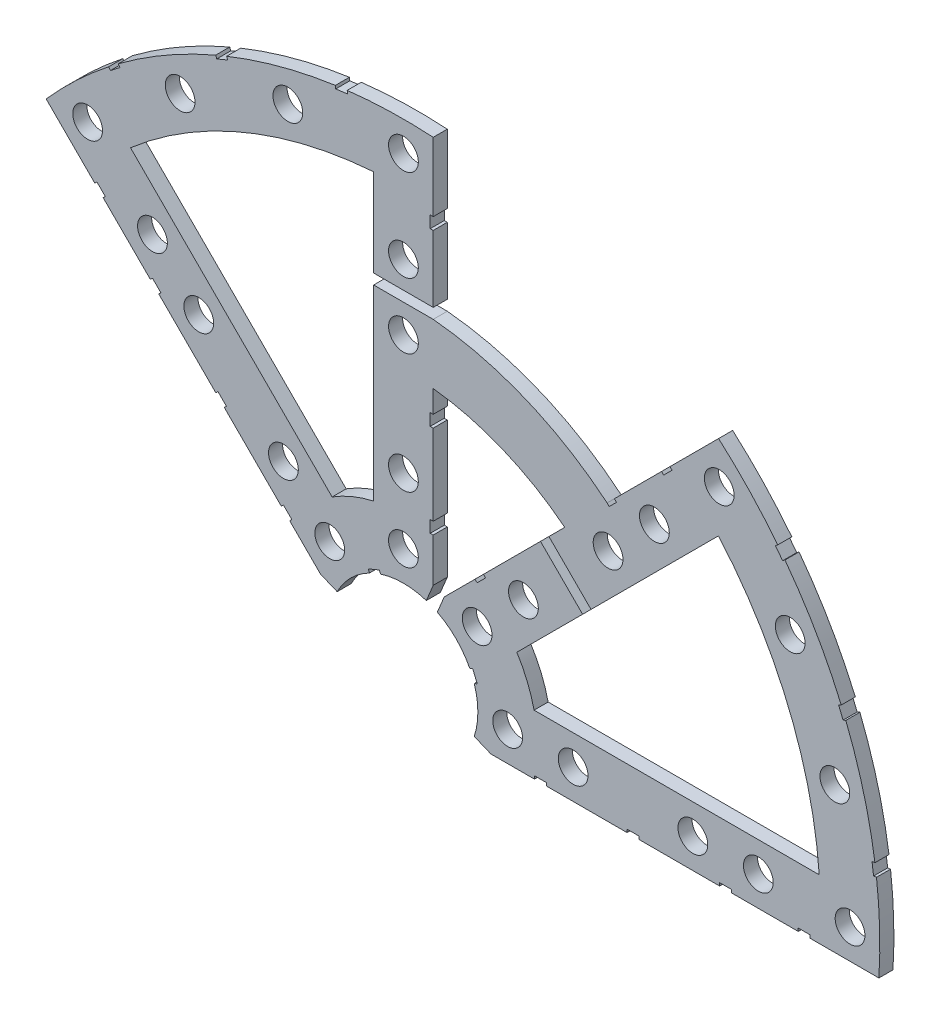
SolidWorks part; units mm, degrees
material "Brass"
ref_plane "Front Plane" through (0, 0, 0) normal (0, 0, 1) x (1, 0, 0)
ref_plane "Top Plane" through (0, 0, 0) normal (0, 1, 0) x (1, 0, 0)
ref_plane "Right Plane" through (0, 0, 0) normal (1, 0, 0) x (0, 0, -1)
sketch "Sketch1" plane through (0, 0, 0) normal (0, 0, 1) x (1, 0, 0)
  line L0 (0, 0) -> (320.3893, 0) construction
  line L1 (0, 0) -> (155.5285, 155.5285) construction
  line L2 (8.6967, 17.6769) -> (34.4055, 43.3857)
  line L3 (8.6967, 17.6769) -> (7.229, 14.1336)
  line L4 (101.4014, -6.35) -> (18.6489, -6.35)
  line L5 (15.1056, -4.8823) -> (18.6489, -6.35)
  line L6 (88.6729, 6.35) -> (27.8605, 6.35)
  line L7 (-76.1917, 67.2115) -> (-17.6769, 8.6967)
  line L8 (-58.2111, 67.1914) -> (-15.2102, 24.1905)
  line L9 (67.1914, 58.2111) -> (24.1905, 15.2102)
  line L10 (0, 0) -> (40.4486, 97.6516) construction
  line L11 (0, 0) -> (123.4567, -51.1374) construction
  line L12 (-6.35, 88.6729) -> (-6.35, 27.8605)
  line L13 (-17.6769, 8.6967) -> (-14.1336, 7.229)
  line L14 (4.8823, 15.1056) -> (6.35, 18.6489)
  line L15 (6.35, 18.6489) -> (6.35, 55.0067)
  line L16 (0, 0) -> (15.1056, -4.8823) construction
  line L17 (0, 0) -> (4.8823, 15.1056) construction
  line L18 (8.6967, 17.6769) -> (13.294, 8.6183) construction
  line L19 (18.6489, -6.35) -> (15.4943, 3.3063) construction
  line L20 (27.8605, 6.35) -> (27.7442, 6.7059) construction
  line L21 (24.1905, 15.2102) -> (24.3599, 14.8764) construction
  line L22 (6.35, 101.4014) -> (6.35, 18.6489) [skipped]
  line L23 (6.35, 67.7752) -> (6.35, 101.4014)
  line L24 (43.4342, 52.4144) -> (67.2115, 76.1917)
  line L25 (67.2115, 76.1917) -> (8.6967, 17.6769) construction
  arc A0 (7.229, 14.1336) -> (15.1056, -4.8823) centre (0, 0) cw
  arc A1 (67.2115, 76.1917) -> (101.4014, -6.35) centre (0, 0) cw
  arc A2 (24.1905, 15.2102) -> (27.8605, 6.35) centre (0, 0) cw
  arc A3 (67.1914, 58.2111) -> (88.6729, 6.35) centre (0, 0) cw
  arc A4 (-76.1917, 67.2115) -> (6.35, 101.4014) centre (0, 0) cw
  arc A5 (-58.2111, 67.1914) -> (-6.35, 88.6729) centre (0, 0) cw
  arc A6 (-15.2102, 24.1905) -> (-6.35, 27.8605) centre (0, 0) cw
  arc A7 (-14.1336, 7.229) -> (4.8823, 15.1056) centre (0, 0) cw
  arc A8 (13.294, 8.6183) -> (15.4943, 3.3063) centre (0, 0) cw construction
  arc A9 (24.3599, 14.8764) -> (27.7442, 6.7059) centre (0, 0) cw construction
  arc A10 (43.4342, 52.4144) -> (6.35, 67.7752) centre (0, 0) ccw
  arc A11 (34.4055, 43.3857) -> (6.35, 55.0067) centre (0, 0) ccw
  dimension "D1" = 45
  dimension "D3" = 6.35
  dimension "D4" = 15.875
  dimension "D7" = 22.5
  dimension "D8" = 101.6
  dimension "D11" = 12.7
  dimension "D12" = 12.7
  dimension "D15" = 12.7
  dimension "D16" = 55.372
  dimension "D2" = 6.35
  dimension "D5" = 67.5
  dimension "D9" = 1.27
  dimension "D10" = 1.27
  dimension "D14" = 90
  dimension "D6" = 12.7
  dimension "D13" = 2
extrude "Boss-Extrude1" add sketch "Sketch1" along normal blind 3
sketch "Sketch2" plane through (0, 0, 3) normal (0, 0, 1) x (1, 0, 0)
  line L0 (0, 0) -> (101.6, 0) construction
  line L1 (0, 0) -> (71.842, 71.842) construction
  line L2 (0, 0) -> (22.225, 0) construction
  line L3 (0, 0) -> (22.225, 0) construction
  line L4 (0, 0) -> (15.7154, 15.7154) construction
  line L5 (0, 0) -> (95.25, 0) construction
  line L6 (0, 0) -> (92.0044, 24.6525) construction
  line L7 (0, 0) -> (0, 22.225) construction
  line L8 (0, 0) -> (92.0044, 24.6525) construction
  line L9 (-76.1917, 67.2115) -> (-17.6769, 8.6967) construction
  line L10 (6.35, 67.7752) -> (6.35, 101.4014) construction
  arc A0 (101.4014, -6.35) -> (67.2115, 76.1917) centre (0, 0) ccw construction
  circle A1 centre (22.225, 0) radius 3.175
  arc A2 (15.1056, -4.8823) -> (7.229, 14.1336) centre (0, 0) ccw construction
  circle A3 centre (36.195, 0) radius 3.175
  circle A4 centre (61.722, 0) radius 3.175
  circle A5 centre (75.692, 0) radius 3.175
  circle A6 centre (95.25, 0) radius 3.175
  circle A7 centre (15.7154, 15.7154) radius 3.175
  circle A8 centre (25.5937, 25.5937) radius 3.175
  circle A9 centre (43.644, 43.644) radius 3.175
  circle A10 centre (53.5223, 53.5223) radius 3.175
  arc A11 (101.4014, -6.35) -> (67.2115, 76.1917) centre (0, 0) ccw construction
  circle A12 centre (92.0044, 24.6525) radius 3.175
  circle A13 centre (82.4889, 47.625) radius 3.175
  circle A14 centre (67.3519, 67.3519) radius 3.175
  circle A15 centre (47.625, 82.4889) radius 3.175 [skipped]
  circle A16 centre (24.6525, 92.0044) radius 3.175 [skipped]
  circle A17 centre (0, 95.25) radius 3.175
  circle A18 centre (0, 75.692) radius 3.175
  circle A19 centre (-53.5223, 53.5223) radius 3.175
  circle A20 centre (-43.644, 43.644) radius 3.175
  circle A21 centre (0, 61.722) radius 3.175
  circle A22 centre (0, 36.195) radius 3.175
  circle A23 centre (-25.5937, 25.5937) radius 3.175
  circle A24 centre (-15.7154, 15.7154) radius 3.175
  circle A25 centre (0, 22.225) radius 3.175
  circle A26 centre (-24.6525, 92.0044) radius 3.175
  circle A27 centre (-47.625, 82.4889) radius 3.175
  circle A28 centre (-67.3519, 67.3519) radius 3.175
  arc A29 (4.8823, 15.1056) -> (-14.1336, 7.229) centre (0, 0) ccw construction
  arc A30 (6.35, 101.4014) -> (-76.1917, 67.2115) centre (0, 0) ccw construction
  dimension "D3" = 6.35
  dimension "D1" = 45
  dimension "D2" = 6.35
  dimension "D5" = 13.97
  dimension "D7" = 13.97
  dimension "D9" = 45
  dimension "D14" = 90
  dimension "D4" = 6.35
  dimension "D8" = 19.558
  dimension "D11" = 15
  dimension "D6" = 25.527
  dimension "D15" = 15
  dimension "D16" = 6.35
  dimension "D17" = 6.35
  dimension "D18" = 6.35
  dimension "D19" = 6.35
  dimension "D20" = 6.35
  dimension "D12" = 2
  dimension "D13" = 2
  dimension "D10" = 10
extrude "Cut-Extrude1" cut sketch "Sketch2" against normal through all
sketch "Sketch3" plane through (0, 0, 3) normal (0, 0, 1) x (1, 0, 0)
  line L0 (15.2664, 24.2467) -> (17.0625, 26.0427)
  line L1 (15.2664, 24.2467) -> (15.7154, 23.7977)
  line L2 (17.0625, 26.0427) -> (17.5115, 25.5937)
  line L3 (15.7154, 23.7977) -> (17.5115, 25.5937)
  line L4 (55.049, 64.0292) -> (56.845, 65.8253)
  line L5 (34.4055, 43.3857) -> (8.6967, 17.6769) construction
  line L6 (29.2307, 38.211) -> (31.0268, 40.007)
  line L7 (29.2307, 38.211) -> (38.211, 29.2307)
  line L8 (31.0268, 40.007) -> (40.007, 31.0268)
  line L9 (27.94, -6.35) -> (30.48, -6.35)
  line L10 (27.94, -6.35) -> (27.94, -5.715)
  line L11 (30.48, -6.35) -> (30.48, -5.715)
  line L12 (27.94, -5.715) -> (30.48, -5.715)
  line L13 (18.6489, -6.35) -> (101.4014, -6.35) construction
  line L14 (67.437, -6.35) -> (69.977, -6.35)
  line L15 (67.437, -6.35) -> (67.437, -5.715)
  line L16 (69.977, -6.35) -> (69.977, -5.715)
  line L17 (67.437, -5.715) -> (69.977, -5.715)
  line L18 (38.211, 29.2307) -> (40.007, 31.0268)
  line L19 (55.049, 64.0292) -> (55.498, 63.5802)
  line L20 (56.845, 65.8253) -> (57.294, 65.3763)
  line L21 (55.498, 63.5802) -> (57.294, 65.3763)
  line L22 (67.2115, 76.1917) -> (43.4342, 52.4144) construction
  line L23 (43.4342, 52.4144) -> (44.9911, 53.9713)
  line L24 (43.4342, 52.4144) -> (43.8832, 51.9654)
  line L25 (44.9911, 53.9713) -> (45.4401, 53.5223)
  line L26 (47.6885, -6.35) -> (50.2285, -6.35)
  line L27 (47.6885, -6.35) -> (47.6885, -5.715)
  line L28 (50.2285, -6.35) -> (50.2285, -5.715)
  line L29 (47.6885, -5.715) -> (50.2285, -5.715)
  line L30 (84.201, -6.35) -> (86.741, -6.35)
  line L31 (84.201, -6.35) -> (84.201, -5.715)
  line L32 (86.741, -6.35) -> (86.741, -5.715)
  line L33 (84.201, -5.715) -> (86.741, -5.715)
  line L34 (0, 0) -> (100.7308, 13.2615) construction
  line L35 (0, 0) -> (93.8662, 38.8806) construction
  line L36 (0, 0) -> (80.6047, 61.8502) construction
  line L37 (0, 0) -> (101.6, 0) construction
  line L38 (99.9355, 14.4377) -> (100.267, 11.9194)
  line L39 (99.9355, 14.4377) -> (101.1946, 14.6035)
  line L40 (100.267, 11.9194) -> (101.5261, 12.0852)
  line L41 (101.1946, 14.6035) -> (101.5261, 12.0852)
  line L42 (99.9355, 14.4377) -> (101.5261, 12.0852) construction
  line L43 (100.267, 11.9194) -> (101.1946, 14.6035) construction
  line L44 (93.7655, 37.4643) -> (94.9388, 37.9503)
  line L45 (93.7655, 37.4643) -> (92.7935, 39.811)
  line L46 (94.9388, 37.9503) -> (93.9668, 40.297)
  line L47 (92.7935, 39.811) -> (93.9668, 40.297)
  line L48 (93.7655, 37.4643) -> (93.9668, 40.297) construction
  line L49 (94.9388, 37.9503) -> (92.7935, 39.811) construction
  line L50 (79.3278, 62.4712) -> (80.874, 60.456)
  line L51 (79.3278, 62.4712) -> (80.3354, 63.2443)
  line L52 (80.874, 60.456) -> (81.8816, 61.2292)
  line L53 (80.3354, 63.2443) -> (81.8816, 61.2292)
  line L54 (79.3278, 62.4712) -> (81.8816, 61.2292) construction
  line L55 (80.874, 60.456) -> (80.3354, 63.2443) construction
  line L56 (13.5939, 7.0054) -> (14.5659, 4.6588)
  line L57 (13.5939, 7.0054) -> (14.7672, 7.4914)
  line L58 (14.5659, 4.6588) -> (15.7393, 5.1448)
  line L59 (14.7672, 7.4914) -> (15.7393, 5.1448)
  line L60 (13.5939, 7.0054) -> (15.7393, 5.1448) construction
  line L61 (14.5659, 4.6588) -> (14.7672, 7.4914) construction
  line L62 (43.8832, 51.9654) -> (45.4401, 53.5223)
  line L63 (6.35, 67.7752) -> (6.35, 69.977)
  line L64 (-40.007, 31.0268) -> (-38.211, 29.2307)
  line L65 (-40.007, 31.0268) -> (-39.558, 31.4758)
  line L66 (-38.211, 29.2307) -> (-37.762, 29.6797)
  line L67 (-39.558, 31.4758) -> (-37.762, 29.6797)
  line L68 (-26.0427, 17.0625) -> (-25.5937, 17.5115)
  line L69 (-23.7977, 15.7154) -> (-25.5937, 17.5115)
  line L70 (-24.2467, 15.2664) -> (-26.0427, 17.0625)
  line L71 (-24.2467, 15.2664) -> (-23.7977, 15.7154)
  line L72 (-65.8253, 56.845) -> (-64.0292, 55.049)
  line L73 (-65.3763, 57.294) -> (-63.5802, 55.498)
  line L74 (-64.0292, 55.049) -> (-63.5802, 55.498)
  line L75 (-65.8253, 56.845) -> (-65.3763, 57.294)
  line L76 (-63.2443, 80.3354) -> (-61.2292, 81.8816)
  line L77 (-62.4712, 79.3278) -> (-61.2292, 81.8816) construction
  line L78 (-60.456, 80.874) -> (-63.2443, 80.3354) construction
  line L79 (-62.4712, 79.3278) -> (-63.2443, 80.3354)
  line L80 (-60.456, 80.874) -> (-61.2292, 81.8816)
  line L81 (-62.4712, 79.3278) -> (-60.456, 80.874)
  line L82 (-37.9503, 94.9388) -> (-40.297, 93.9668)
  line L83 (-37.4643, 93.7655) -> (-40.297, 93.9668) construction
  line L84 (-37.9503, 94.9388) -> (-39.811, 92.7935) construction
  line L85 (-39.811, 92.7935) -> (-40.297, 93.9668)
  line L86 (-37.4643, 93.7655) -> (-37.9503, 94.9388)
  line L87 (-37.4643, 93.7655) -> (-39.811, 92.7935)
  line L88 (-14.4377, 99.9355) -> (-14.6035, 101.1946)
  line L89 (-14.4377, 99.9355) -> (-11.9194, 100.267)
  line L90 (-14.4377, 99.9355) -> (-12.0852, 101.5261) construction
  line L91 (-11.9194, 100.267) -> (-14.6035, 101.1946) construction
  line L92 (-11.9194, 100.267) -> (-12.0852, 101.5261)
  line L93 (-14.6035, 101.1946) -> (-12.0852, 101.5261)
  line L94 (5.715, 84.201) -> (5.715, 86.741)
  line L95 (6.35, 86.741) -> (5.715, 86.741)
  line L96 (6.35, 84.201) -> (6.35, 86.741)
  line L97 (6.35, 84.201) -> (5.715, 84.201)
  line L98 (5.715, 47.6885) -> (5.715, 50.2285)
  line L99 (6.35, 47.6885) -> (6.35, 50.2285)
  line L100 (6.35, 47.6885) -> (5.715, 47.6885)
  line L101 (6.35, 50.2285) -> (5.715, 50.2285)
  line L102 (5.715, 27.94) -> (5.715, 30.48)
  line L103 (6.35, 27.94) -> (6.35, 30.48)
  line L104 (6.35, 30.48) -> (5.715, 30.48)
  line L105 (6.35, 27.94) -> (5.715, 27.94)
  line L106 (-7.4914, 14.7672) -> (-5.1448, 15.7393)
  line L107 (-7.0054, 13.5939) -> (-5.1448, 15.7393) construction
  line L108 (-4.6588, 14.5659) -> (-7.4914, 14.7672) construction
  line L109 (-7.0054, 13.5939) -> (-4.6588, 14.5659)
  line L110 (-7.0054, 13.5939) -> (-7.4914, 14.7672)
  line L111 (-4.6588, 14.5659) -> (-5.1448, 15.7393)
  line L112 (0, 0) -> (14.5659, 4.6588) construction
  line L113 (0, 0) -> (-4.6588, 14.5659) construction
  line L114 (6.35, 67.7752) -> (-6.35, 67.7752)
  line L115 (6.35, 69.977) -> (-6.35, 69.977)
  line L116 (-6.35, 67.7752) -> (-6.35, 69.977)
  line L117 (6.35, 67.7752) -> (6.35, 101.4014) construction
  line L120 (-53.9713, 44.9911) -> (-52.1753, 43.195)
  line L121 (-53.9713, 44.9911) -> (-53.5223, 45.4401)
  line L122 (-52.1753, 43.195) -> (-51.7263, 43.644)
  line L123 (-53.5223, 45.4401) -> (-51.7263, 43.644)
  line L124 (-76.1917, 67.2115) -> (-17.6769, 8.6967) construction
  line L125 (-38.211, 29.2307) -> (-40.007, 31.0268) [skipped]
  line L126 (-40.007, 31.0268) -> (-31.0268, 40.007) [skipped]
  line L127 (-29.2307, 38.211) -> (-31.0268, 40.007) [skipped]
  line L128 (-38.211, 29.2307) -> (-29.2307, 38.211) [skipped]
  circle A0 centre (53.5223, 53.5223) radius 3.175 construction
  circle A1 centre (0, 75.692) radius 3.175 construction
  circle A2 centre (22.225, 0) radius 3.175 construction
  circle A3 centre (61.722, 0) radius 3.175 construction
  arc A4 (101.4014, -6.35) -> (67.2115, 76.1917) centre (0, 0) ccw construction
  circle A6 centre (-43.644, 43.644) radius 3.175 construction
  arc A9 (15.1056, -4.8823) -> (7.229, 14.1336) centre (0, 0) ccw construction
  circle A10 centre (15.7154, 15.7154) radius 3.175 construction
  circle A12 centre (-15.7154, 15.7154) radius 3.175 construction
  circle A13 centre (36.195, 0) radius 3.175 construction
  circle A14 centre (75.692, 0) radius 3.175 construction
  circle A15 centre (25.5937, 25.5937) radius 3.175 construction
  circle A16 centre (-25.5937, 25.5937) radius 3.175 construction
  circle A17 centre (0, 36.195) radius 3.175 construction
  circle A18 centre (-53.5223, 53.5223) radius 3.175 construction
  point P75 (14.6666, 6.0751)
  dimension "D9" = 5.715
  dimension "D12" = 5.715
  dimension "D4" = 7.5
  dimension "D5" = 22.5
  dimension "D7" = 37.5
  dimension "D10" = 90
  dimension "D11" = 1.27
  dimension "D14" = 0.635
  dimension "D15" = 90
  dimension "D18" = 0.635
  dimension "D19" = 90
  dimension "D22" = 0.635
  dimension "D20" = 1.27
  dimension "D17" = 0.635
  dimension "D3" = 5.715
  dimension "D25" = 90
  dimension "D26" = 2.54
  dimension "D28" = 5.715
  dimension "D21" = 0.635
  dimension "D30" = 12.7
  dimension "D31" = 5.715
  dimension "D33" = 5.715
  dimension "D34" = 12.7
  dimension "D38" = 5.715
  dimension "D6" = 11.4935
  dimension "D13" = 8.509
  dimension "D16" = 11.4935
  dimension "D23" = 8.509
  dimension "D37" = 11.4935
  dimension "D39" = 11.4935
  dimension "D40" = 8.509
  dimension "D41" = 8.509
  dimension "D42" = 2.54
  dimension "D8" = 90
  dimension "D24" = 2
extrude "Cut-Extrude2" cut sketch "Sketch3" against normal through all
equation "\"LayerH\"= 3mm"
equation "\"D1@Boss-Extrude1\"=\"LayerH\""
equation "\"CoilSep\"= 1.005"
equation "\"D6@Sketch2\"=\"CoilSep\""
equation "\"CoilSep2\"= \"D8@Sketch2\""
equation "\"D6@Sketch3\"=\"CoilSep\"/2-.05"
equation "\"D13@Sketch3\"=\"CoilSep2\"/2-.05"
equation "\"D16@Sketch3\"=\"CoilSep\"/2-.05"
equation "\"D23@Sketch3\"=\"CoilSep2\"/2-.05"
equation "\"D37@Sketch3\"=\"CoilSep\"/2-.05"
equation "\"D39@Sketch3\"=\"CoilSep\"/2-.05"
equation "\"D41@Sketch3\"=\"CoilSep2\"/2-.05"
